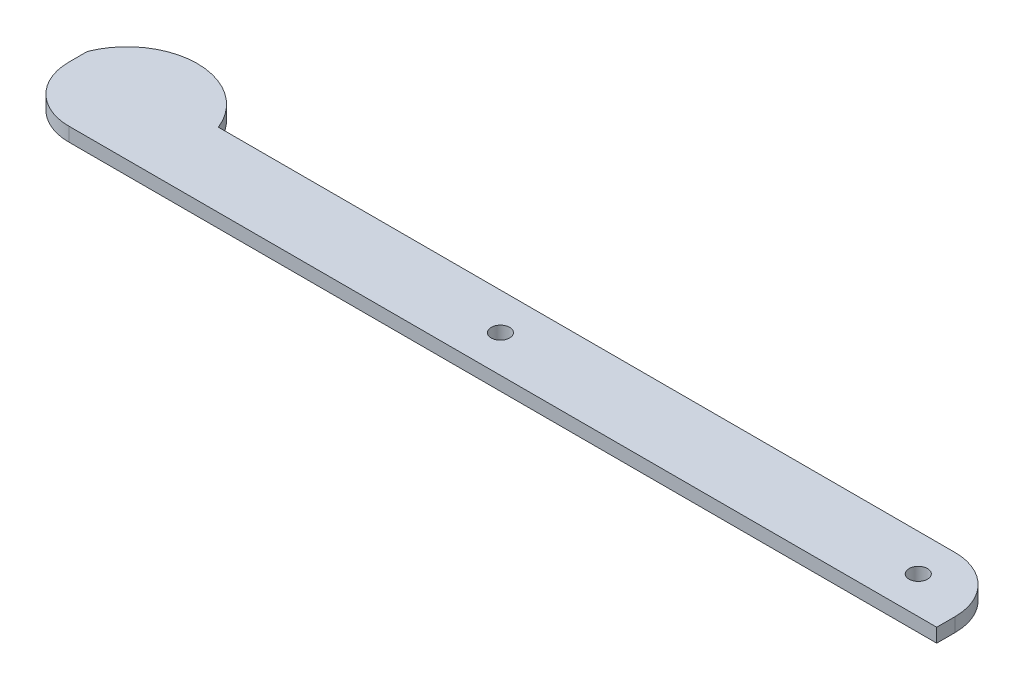
SolidWorks part; units mm, degrees
material "Pine"
ref_plane "Front Plane" through (0, 0, 0) normal (0, 0, 1) x (1, 0, 0)
ref_plane "Top Plane" through (0, 0, 0) normal (0, 1, 0) x (1, 0, 0)
ref_plane "Right Plane" through (0, 0, 0) normal (1, 0, 0) x (0, 0, -1)
sketch "Sketch1" plane through (0, 0, 0) normal (0, 1, 0) x (1, 0, 0)
  line L1 (-558.8, -50.8) -> (635, -50.8)
  line L2 (-635, 25.4) -> (-635, 50.8)
  line L3 (-454.6566, 50.8) -> (558.8, 50.8)
  line L4 (635, -50.8) -> (635, -25.4)
  line L5 (-635, -50.8) -> (635, 50.8) construction
  line L6 (-28.4346, 2.2748) -> (635, -50.8) construction
  circle A0 centre (-15.94, 0) radius 12.7
  circle A1 centre (558.8, 0) radius 12.7
  arc A2 (558.8, 50.8) -> (635, -25.4) centre (558.8, -25.4) cw
  arc A3 (-558.8, -50.8) -> (-635, 25.4) centre (-558.8, 25.4) cw
  arc A4 (-635, 50.8) -> (-454.6566, 50.8) centre (-544.8283, 15.1679) cw
  point P0 (0, 0)
  dimension "D4" = 25.4
  dimension "D5" = 25.4
  dimension "D7" = 76.2
  dimension "D1" = 101.6
  dimension "D2" = 1270
  dimension "D3" = 574.74
  dimension "D6" = 76.2
extrude "Boss-Extrude1" add sketch "Sketch1" along normal blind 19.05
